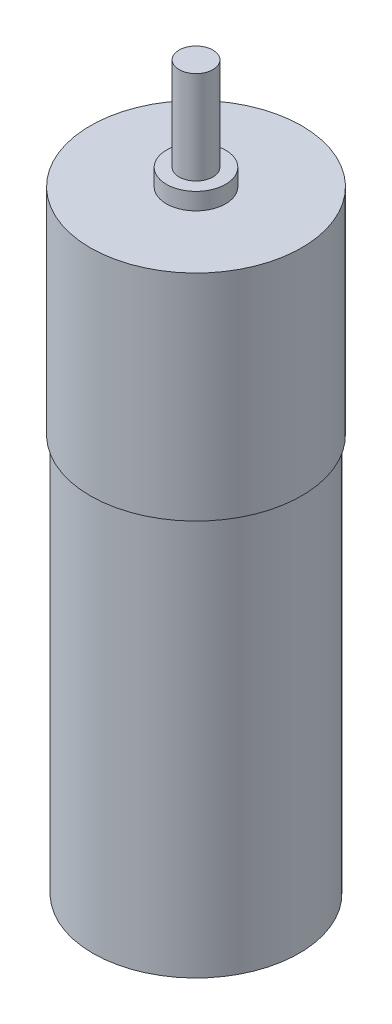
SolidWorks part; units mm, degrees
ref_plane "Front Plane" through (0, 0, 0) normal (0, 0, 1) x (1, 0, 0)
ref_plane "Top Plane" through (0, 0, 0) normal (0, 1, 0) x (1, 0, 0)
ref_plane "Right Plane" through (0, 0, 0) normal (1, 0, 0) x (0, 0, -1)
sketch "Sketch1" plane through (0, 0, 0) normal (0, 1, 0) x (1, 0, 0)
  circle A0 centre (0, 0) radius 12.2
  dimension "D1" = 24.4
extrude "Boss-Extrude1" add sketch "Sketch1" along normal blind 47
sketch "Sketch2" plane through (0, 47, 0) normal (0, 1, 0) x (1, 0, 0)
  circle A0 centre (0, 0) radius 12.5
extrude "Boss-Extrude2" add sketch "Sketch2" along normal blind 25.4
sketch "Sketch3" plane through (0, 72.4, 0) normal (0, 1, 0) x (1, 0, 0)
  circle A0 centre (0, 0) radius 3.5
extrude "Boss-Extrude3" add sketch "Sketch3" along normal blind 2
sketch "Sketch4" plane through (0, 74.4, 0) normal (0, 1, 0) x (1, 0, 0)
  circle A0 centre (0, 0) radius 2
extrude "Boss-Extrude4" add sketch "Sketch4" along normal blind 11
